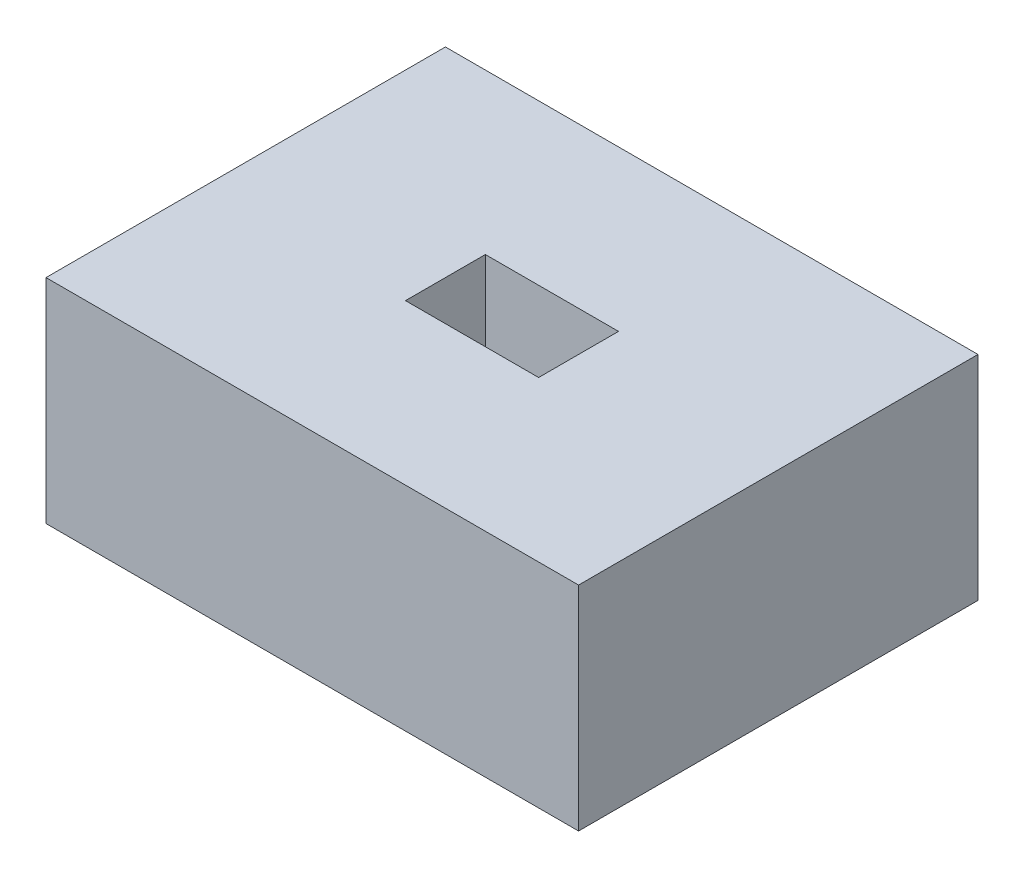
SolidWorks part; units mm, degrees
ref_plane "Front" through (0, 0, 0) normal (0, 0, 1) x (1, 0, 0)
ref_plane "Top" through (0, 0, 0) normal (0, 1, 0) x (1, 0, 0)
ref_plane "Right" through (0, 0, 0) normal (1, 0, 0) x (0, 0, -1)
sketch "Sketch1" plane through (0, 0, 0) normal (0, 1, 0) x (1, 0, 0)
  line L5 (-10, -7.5) -> (10, -7.5)
  line L6 (-10, -7.5) -> (-10, 7.5)
  line L11 (-10, 7.5) -> (10, 7.5)
  line L12 (10, -7.5) -> (10, 7.5)
  line L13 (-10, -7.5) -> (10, 7.5) construction
  line L14 (-10, 7.5) -> (10, -7.5) construction
  point P0 (0, 0)
  dimension "D1" = 15
  dimension "D2" = 20
extrude "Boss-Extrude1" add sketch "Sketch1" along normal blind 8
sketch "Sketch2" plane through (0, 8, 0) normal (0, 1, 0) x (1, 0, 0)
  line L1 (-2.5, -1.5) -> (2.5, -1.5)
  line L2 (-2.5, -1.5) -> (-2.5, 1.5)
  line L3 (-2.5, 1.5) -> (2.5, 1.5)
  line L4 (2.5, -1.5) -> (2.5, 1.5)
  line L5 (-2.5, -1.5) -> (2.5, 1.5) construction
  line L6 (-2.5, 1.5) -> (2.5, -1.5) construction
  point P0 (0, 0)
  dimension "D1" = 3
  dimension "D2" = 5
extrude "Cut-Extrude1" cut sketch "Sketch2" against normal blind 3.2
sketch "Sketch3" plane through (0, 0, 0) normal (0, -1, 0) x (1, 0, 0)
  line L8 (2.5, -1.5) -> (2.5, 1.5)
  line L9 (-2.5, -1.5) -> (2.5, -1.5)
  line L10 (-2.5, 1.5) -> (-2.5, -1.5)
  line L11 (2.5, 1.5) -> (-2.5, 1.5)
  line L12 (2.5, -1.5) -> (2.5, 1.5)
  line L13 (-2.5, -1.5) -> (2.5, -1.5)
  line L14 (-2.5, 1.5) -> (-2.5, -1.5)
  line L15 (2.5, 1.5) -> (-2.5, 1.5)
  dimension "D1" = 0
extrude "Boss-Extrude2" add sketch "Sketch3" along normal blind 3
